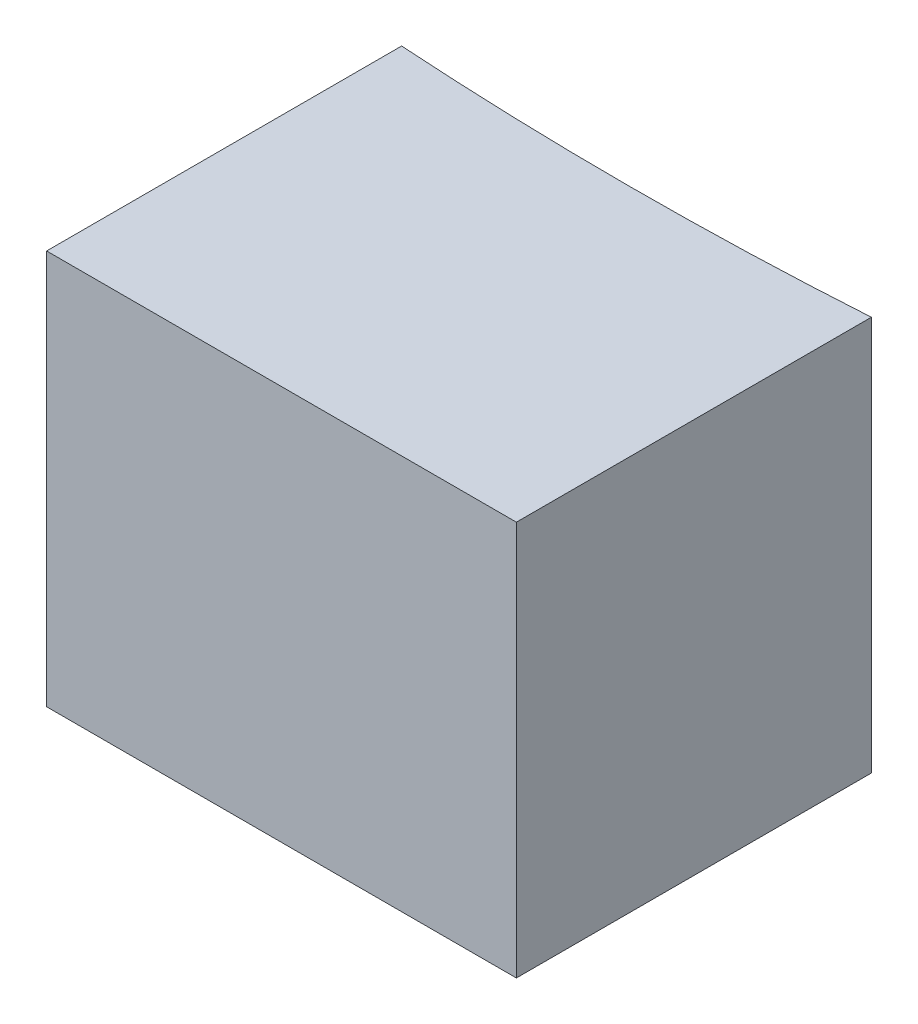
SolidWorks part; units mm, degrees
material "AISI 304"
ref_plane "Front Plane" through (0, 0, 0) normal (0, 0, 1) x (1, 0, 0)
ref_plane "Top Plane" through (0, 0, 0) normal (0, 1, 0) x (1, 0, 0)
ref_plane "Right Plane" through (0, 0, 0) normal (1, 0, 0) x (0, 0, -1)
sketch "Sketch1" plane through (0, 0, 0) normal (0, 1, 0) x (1, 0, 0)
  line L0 (0, 0) -> (0, -233.553) construction
  line L1 (15.113, -233.0635) -> (15.113, -255.905)
  line L2 (15.113, -255.905) -> (-15.113, -255.905)
  line L3 (-15.113, -255.905) -> (-15.113, -233.0635)
  circle A0 centre (0, 0) radius 233.553 construction
  arc A1 (15.113, -233.0635) -> (-15.113, -233.0635) centre (0, 0) cw
  dimension "D1" = 22.352
  dimension "D2" = 30.226
extrude "Boss-Extrude1" add sketch "Sketch1" along normal blind 25.4
